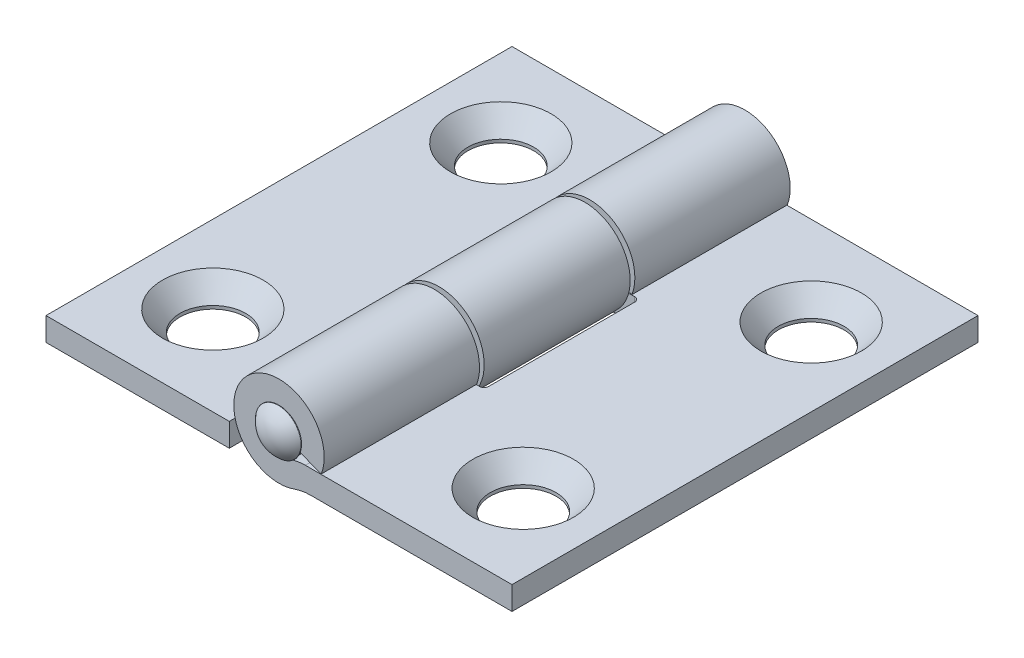
SolidWorks part; units mm, degrees
ref_plane "Front Plane" through (0, 0, 0) normal (0, 0, 1) x (1, 0, 0)
ref_plane "Top Plane" through (0, 0, 0) normal (0, 1, 0) x (1, 0, 0)
ref_plane "Right Plane" through (0, 0, 0) normal (1, 0, 0) x (0, 0, -1)
sketch "Sketch1" plane through (0, 0, 0) normal (0, 0, 1) x (1, 0, 0)
  line L0 (12.7, -2.1622) -> (1.1811, -2.1622)
  line L1 (12.7, -2.1622) -> (12.7, -0.8922)
  line L2 (12.7, -0.8922) -> (2.2966, -0.8922)
  line L3 (1.1811, -2.1622) -> (1.1811, 0) construction
  line L4 (-2.4638, 0) -> (-2.4638, -2.1622) construction
  line L5 (-12.7, -0.8922) -> (-2.8448, -0.8922)
  line L6 (-12.7, -0.8922) -> (-12.7, -2.1622)
  line L7 (-12.7, -2.1622) -> (-2.8448, -2.1622)
  line L8 (-2.8448, -0.8922) -> (-2.8448, -2.1622)
  line L9 (-2.4638, -2.1622) -> (-2.4638, -12.0174) construction
  circle A0 centre (0, 0) radius 1.1811
  arc A1 (1.1811, -2.1622) -> (2.2966, -0.8922) centre (0, 0) cw
  point P5 (-1.1811, 0)
  point P15 (2.4638, 0)
  point P16 (-12.7, -2.1622)
  point P17 (12.7, -2.1622)
  point P18 (1.1811, 0)
  point P19 (1.1811, 0)
  point P21 (12.7, -0.8922)
  point P22 (-12.7, -0.8922)
  point P24 (-2.4638, 0)
  dimension "knuckle dia" = 4.9276
  dimension "Leaf Thickness" = 1.27
  dimension "D3" = 0.381
  dimension "Overall Width" = 25.4
  dimension "Range of Motion" = 270
sketch "Sketch2" plane through (0, 0, 0) normal (1, 0, 0) x (0, 0, -1)
  line L0 (-12.7, 0) -> (12.7, 0)
  point P2 (0, 0)
  point P6 (12.7, 0)
  point P7 (-12.7, 0)
  dimension "Frame Leaf Height" = 25.4
ref_plane "Plane1" through (0, -2.1622, 0) normal (0, 1, 0) x (1, 0, 0)
sketch "Sketch3" plane through (0, -2.1622, 0) normal (0, 1, 0) x (1, 0, 0)
  line L0 (8.4582, 7.8486) -> (9.6369, 9.1967) construction
  line L1 (12.7, -12.7) -> (-12.7, -12.7)
  line L2 (12.7, -12.7) -> (12.7, 12.7)
  line L3 (12.7, 12.7) -> (-12.7, 12.7)
  line L4 (-12.7, -12.7) -> (-12.7, 12.7)
  line L5 (-8.4582, 7.8486) -> (8.4582, 7.8486) construction
  line L6 (-8.4582, 7.8486) -> (-8.4582, -7.8486) construction
  line L7 (-8.4582, -7.8486) -> (8.4582, -7.8486) construction
  line L8 (8.4582, 7.8486) -> (8.4582, -7.8486) construction
  circle A0 centre (-8.4582, 7.8486) radius 1.7907
  circle A1 centre (8.4582, 7.8486) radius 1.7907
  circle A2 centre (8.4582, -7.8486) radius 1.7907
  circle A3 centre (-8.4582, -7.8486) radius 1.7907
  circle A4 centre (-8.4582, 7.8486) radius 2.7432
  point P0 (0, 0)
  point P6 (-12.7, 0)
  point P14 (8.4582, 0)
  point P15 (0, 7.8486)
  point P20 (0, -12.7)
  point P21 (-12.7, 12.7)
  point P22 (12.7, 12.7)
  point P23 (12.7, -12.7)
  point P24 (-12.7, -12.7)
  point P25 (-8.4582, -7.8486)
  point P26 (8.4582, -7.8486)
  point P27 (8.4582, 7.8486)
  point P28 (-8.4582, 7.8486)
  point P29 (12.7, 0)
  point P30 (0, 12.7)
  point P32 (9.6369, 9.1967)
  dimension "Mounting Hole Dia" = 3.5814
  dimension "Countersink Diameter" = 5.4864
  dimension "CTC Hole Ht" = 15.6972
  dimension "Center Hole Wd" = 8.4582
sketch "Sketch4" plane through (0, 0, 0) normal (0, 0, 1) x (1, 0, 0)
  line L4 (12.7, -2.1622) -> (12.7, -0.8922) construction
  line L5 (12.7, -2.1622) -> (1.1811, -2.1622) construction
  line L6 (12.7, -0.8922) -> (2.2966, -0.8922) construction
  line L11 (12.7, -2.1622) -> (12.7, -0.8922)
  line L12 (12.7, -2.1622) -> (1.7108, -2.1622)
  line L13 (12.7, -0.8922) -> (1.4375, -0.8922)
  line L14 (2.3063, -0.8668) -> (1.1056, -0.4156)
  circle A0 centre (0, 0) radius 1.1811 construction
  arc A1 (2.2966, -0.8922) -> (1.1811, -2.1622) centre (0, 0) ccw construction
  arc A2 (1.1056, -0.4156) -> (0.4563, -1.0894) centre (0, 0) ccw
  arc A3 (2.3063, -0.8668) -> (0.8424, -2.3153) centre (0, 0) ccw
  arc A4 (1.4375, -0.8922) -> (0.4563, -1.0894) centre (1.4375, -3.4322) ccw
  arc A5 (1.7108, -2.1622) -> (0.8424, -2.3153) centre (1.7108, -4.7022) ccw
  dimension "D2" = 2.54
  dimension "D1" = 0.0254
extrude "Boss-Extrude1" add sketch "Sketch4" against normal up to vertex (12.7 mm away) and the other way up to vertex (12.7 mm away) up to point (-12.7, -2.1622, -12.7) other way up to point (-12.7, -2.1622, 12.7)
sketch "Sketch5" plane through (0, 0, 0) normal (0, 1, 0) x (1, 0, 0)
  line L0 (0, 13.335) -> (0, 12.7) construction
  line L2 (12.7, 12.7) -> (-12.7, 12.7) construction
  line L3 (-1.2181, 12.7) -> (-1.1811, 12.7)
  line L4 (-1.1811, 12.7) -> (-1.1811, -12.7)
  line L5 (12.7, -12.7) -> (-12.7, -12.7) construction
  line L8 (0, 13.335) -> (0, -13.335)
  line L10 (-2.4638, 0) -> (2.4638, 0) construction
  line L11 (-2.4638, 0) -> (0, 0) construction
  line L12 (-1.2181, -12.7) -> (-1.1811, -12.7)
  circle A0 centre (0, 13.0175) radius 0.3175 construction
  arc A1 (0, 13.335) -> (-1.2379, 12.7413) centre (0, 11.7475) ccw
  arc A2 (-1.2379, -12.7413) -> (0, -13.335) centre (0, -11.7475) ccw
  arc A3 (-1.2379, 12.7413) -> (-1.2181, 12.7) centre (-1.2181, 12.7254) ccw
  arc A5 (-1.2181, -12.7) -> (-1.2379, -12.7413) centre (-1.2181, -12.7254) ccw
  point P2 (0, 13.335)
  point P20 (0, 0)
  point P21 (-1.1811, 0)
  dimension "D2" = 1.5875
  dimension "D4" = 0.0254
  dimension "D1" = 0.635
  dimension "D3" = 25.4
revolve "Revolve1" add sketch "Sketch5" angle 360 about L8
sketch "Sketch6" plane through (0, -0.8922, 0) normal (0, 1, 0) x (1, 0, 0)
  circle A2 centre (8.4582, -7.8486) radius 1.7907 construction
  circle A3 centre (8.4582, 7.8486) radius 1.7907 construction
  circle A6 centre (8.4582, -7.8486) radius 1.7907
  circle A7 centre (8.4582, 7.8486) radius 1.7907
extrude "Cut-Extrude1" cut sketch "Sketch6" against normal blind 2.54
sketch "Sketch11" plane through (0, -0.8922, 0) normal (0, 1, 0) x (1, 0, 0)
  circle A0 centre (8.4582, 7.8486) radius 2.7432
  circle A1 centre (8.4582, -7.8486) radius 2.7432
  circle A2 centre (-8.4582, 7.8486) radius 2.7432 construction
extrude "Cut-Extrude5" cut sketch "Sketch11" against normal through all draft 41
mirror "Mirror1" about plane through (0, 0, 0) normal (1, 0, 0) of bodies 157
sketch "Sketch8" plane through (0, -2.1622, 0) normal (0, 1, 0) x (1, 0, 0)
  line L1 (-2.7102, 4.2333) -> (2.7102, 4.2333)
  line L2 (-2.7102, 4.2333) -> (-2.7102, -4.2333)
  line L3 (-2.7102, -4.2333) -> (2.7102, -4.2333)
  line L4 (2.7102, 4.2333) -> (2.7102, -4.2333)
  line L5 (0, 12.7) -> (0, 4.2333) construction
  line L6 (0, -4.2333) -> (0, -12.7) construction
  point P6 (0, 4.2333)
  dimension "D1" = 5.4204
extrude "Cut-Extrude2" cut sketch "Sketch8" against normal through all both and the other way through all
sketch "Sketch12" plane through (0, -0.8922, 0) normal (0, 1, 0) x (1, 0, 0)
  line L0 (2.7102, 4.2333) -> (2.7102, -4.2333) construction
  line L1 (2.7102, 3.9793) -> (-2.7102, 3.9793)
  line L2 (2.7102, 3.9793) -> (2.7102, 12.7)
  line L3 (2.7102, 12.7) -> (-2.7102, 12.7)
  line L4 (-2.7102, 3.9793) -> (-2.7102, 12.7)
  line L5 (2.7102, -3.9793) -> (-2.7102, -3.9793)
  line L6 (2.7102, -3.9793) -> (2.7102, -12.7)
  line L7 (2.7102, -12.7) -> (-2.7102, -12.7)
  line L8 (-2.7102, -3.9793) -> (-2.7102, -12.7)
  line L9 (-2.7102, 4.2333) -> (-2.7102, -4.2333) construction
  line L10 (2.7102, -3.9793) -> (2.7102, -4.2333) construction
  line L11 (2.7102, 4.2333) -> (2.7102, 3.9793) construction
  line L12 (2.7102, -4.2333) -> (2.7102, 4.2333) construction
  dimension "D1" = 0.254
extrude "Cut-Extrude6" cut sketch "Sketch12" against normal through all both and the other way through all
fillet "Fillet1" radius 0.254 2 edges at (-2.7102, -1.5272, -3.9793) (-2.7102, -1.5272, 3.9793)
fillet "Fillet2" radius 0.254 2 edges at (2.7102, -1.5272, 4.2333) (2.7102, -1.5272, -4.2333)
sketch "Sketch13" plane through (0, -0.8922, 0) normal (0, 1, 0) x (1, 0, 0)
  line L0 (-12.7, 12.7) -> (-12.7, -12.7)
  line L1 (-12.7, 12.7) -> (-2.7102, 12.7)
  dimension "D1" = 9.9898
  dimension "D2" = 25.4
equation "\"Overall Width@Sketch1\"=\"Frame Leaf Width@Sketch1\"*2"
equation "\"D1@Sketch5\"=\"Leaf Thickness@Sketch1\" * .5"
equation "\"D2@Sketch5\"=\"D1@Sketch5\"*2.5"
equation "\"D1@Sketch8\"=\"knuckle dia@Sketch1\"*1.1"
